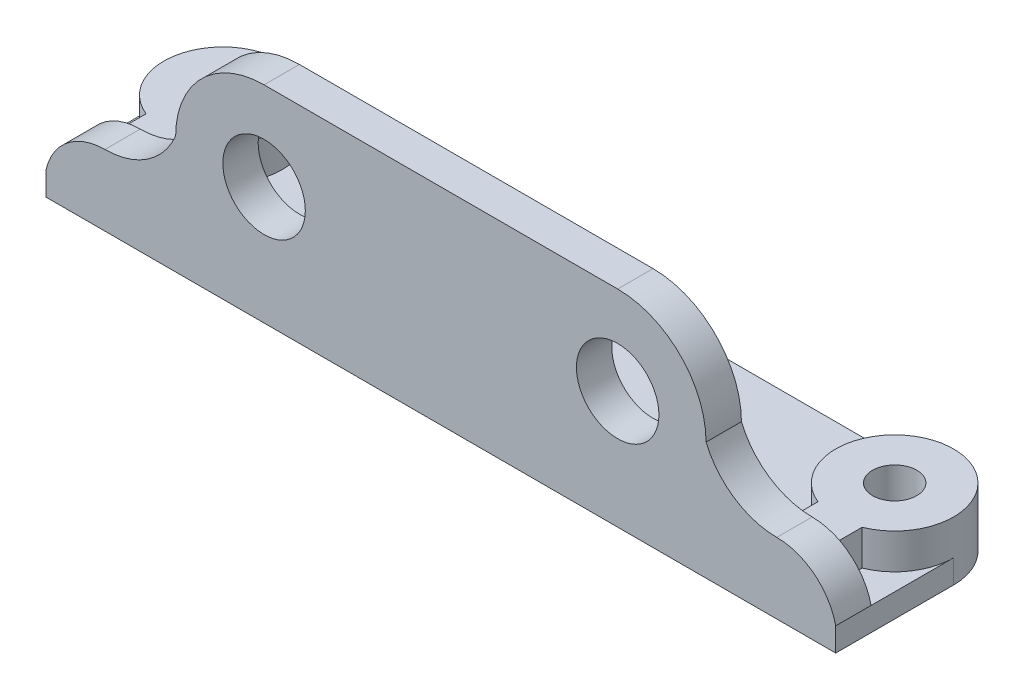
SolidWorks part; units mm, degrees
ref_plane "Front Plane" through (0, 0, 0) normal (0, 0, 1) x (1, 0, 0)
ref_plane "Top Plane" through (0, 0, 0) normal (0, 1, 0) x (1, 0, 0)
ref_plane "Right Plane" through (0, 0, 0) normal (1, 0, 0) x (0, 0, -1)
sketch "Sketch1" plane through (0, 0, 0) normal (0, 1, 0) x (1, 0, 0)
  line L0 (0, 0) -> (57, 0) construction
  line L1 (-5, -5) -> (62, -5)
  line L2 (0, 5) -> (57, 5)
  line L3 (-5, 0) -> (-5, -10)
  line L4 (-5, -10) -> (62, -10)
  line L5 (62, 0) -> (62, -10)
  line L6 (5, 5) -> (5, -5)
  line L7 (52, 5) -> (52, -5)
  circle A0 centre (0, 0) radius 1.875
  circle A1 centre (57, 0) radius 1.875
  arc A2 (62, 0) -> (57, 5) centre (57, 0) ccw
  arc A3 (-5, 0) -> (0, 5) centre (0, 0) cw
  dimension "D2" = 3.75
  dimension "D3" = 3.75
  dimension "D8" = 5
  dimension "D1" = 57
  dimension "D4" = 5
  dimension "D5" = 5
  dimension "D6" = 5
  dimension "D7" = 10
  dimension "D9" = 10
  dimension "D10" = 5
extrude "Boss-Extrude1" add sketch "Sketch1" along normal blind 2
sketch "Sketch2" plane through (0, 2, 0) normal (0, 1, 0) x (1, 0, 0)
  line L0 (62, 0) -> (62, -10) construction
  line L1 (-5, -10) -> (62, -10)
  line L2 (-5, -10) -> (-5, -7)
  line L3 (-5, -7) -> (62, -7)
  line L4 (62, -10) -> (62, -7)
  line L5 (28.5, -10) -> (28.5, 1.6847) construction
  line L6 (-1.875, 0) -> (1.875, 0)
  line L7 (-1.875, 0) -> (-1.875, -10)
  line L8 (-1.875, -10) -> (1.875, -10)
  line L9 (1.875, 0) -> (1.875, -10)
  line L10 (58.875, 0) -> (58.875, -10)
  line L11 (55.125, 0) -> (55.125, -10)
  circle A0 centre (57, 0) radius 1.875 construction
  circle A1 centre (0, 0) radius 1.875 construction
  circle A2 centre (57, 0) radius 1.875
  circle A3 centre (0, 0) radius 1.875
  circle A4 centre (0, 0) radius 5
  circle A5 centre (57, 0) radius 5
  arc M8 (62, 0) -> (57, 5) centre (57, 0) ccw
  arc M10 (0, 5) -> (-5, 0) centre (0, 0) ccw
  line M11 (-5, 0) -> (-5, -10)
  line M12 (-5, -10) -> (62, -10)
  line M13 (62, -10) -> (62, 0)
  circle M14 centre (57, 0) radius 1.875
  circle M15 centre (0, 0) radius 1.875
  dimension "D1" = 3
extrude "Boss-Extrude2" add sketch "Sketch2" along normal blind 3 contours L9 A4 L7 M10 M15 | L7 A4 L9 M15 | A4 L7 L3 L9 | L7 L3 M11 M12 | L9 L3 L7 L1 | L5 L3 L9 M12 | L10 A5 L11 M8 M14 | L11 A5 L10 M14 | A5 L11 L3 L10 | L3 L10 L1 M13 | L3 L11 L1 L10 | L5 L1 L11 L3
sketch "Sketch3" plane through (0, 5, 0) normal (0, 1, 0) x (1, 0, 0)
  line L1 (-5, -7) -> (62, -7)
  line L2 (-5, -7) -> (-5, -10)
  line L3 (-5, -10) -> (62, -10)
  line L4 (62, -7) -> (62, -10)
extrude "Boss-Extrude3" add sketch "Sketch3" along normal blind 20
sketch "Sketch4" plane through (0, 0, 10) normal (0, 0, 1) x (1, 0, 0)
  line L0 (-5, 2) -> (-5, 0)
  line L1 (6, 10) -> (-5, 10)
  line L2 (-5, 10) -> (-5, 2)
  line L3 (0, 2) -> (57, 2) construction
  line L4 (0, 2) -> (57, 2)
  line L5 (57, 2) -> (62, 2)
  line L6 (62, 25) -> (62, 0) construction
  line L7 (0, 2) -> (-5, 2)
  line L8 (-5, 25) -> (-5, 0) construction
  line L9 (28.5, 0) -> (28.5, 25) construction
  line L10 (-5, 0) -> (62, 0) construction
  line L11 (-5, 25) -> (62, 25) construction
  line L12 (13.5, 0) -> (13.5, 10) construction
  line L13 (-5, 6) -> (7.1557, 6)
  line L14 (0, 2) -> (0, 6)
  line L15 (13.5, 17.5) -> (43.5, 17.5)
  circle A0 centre (13.5, 10) radius 3.5
  circle A1 centre (13.5, 10) radius 7.5
  arc A2 (0, 6) -> (-5, 2) centre (0, 0.875) ccw
  arc A3 (0, 6) -> (6, 10) centre (0, 12.5) ccw
  arc A4 (57, 6) -> (62, 2) centre (57, 0.875) cw
  arc A5 (57, 6) -> (51, 10) centre (57, 12.5) cw
  circle A6 centre (43.5, 10) radius 3.5
  circle A7 centre (43.5, 10) radius 7.5
  point P40 (28.5, 17.5)
  dimension "D3" = 7
  dimension "D1" = 10
  dimension "D2" = 15
  dimension "D4" = 4
extrude "Cut-Extrude1" cut sketch "Sketch4" against normal up to next contours L15 A7 A5 A4 L3 L4 L5 L1 A1 | A0 | A6 | L13 A3 L1 L5 | A2 L13 L2
